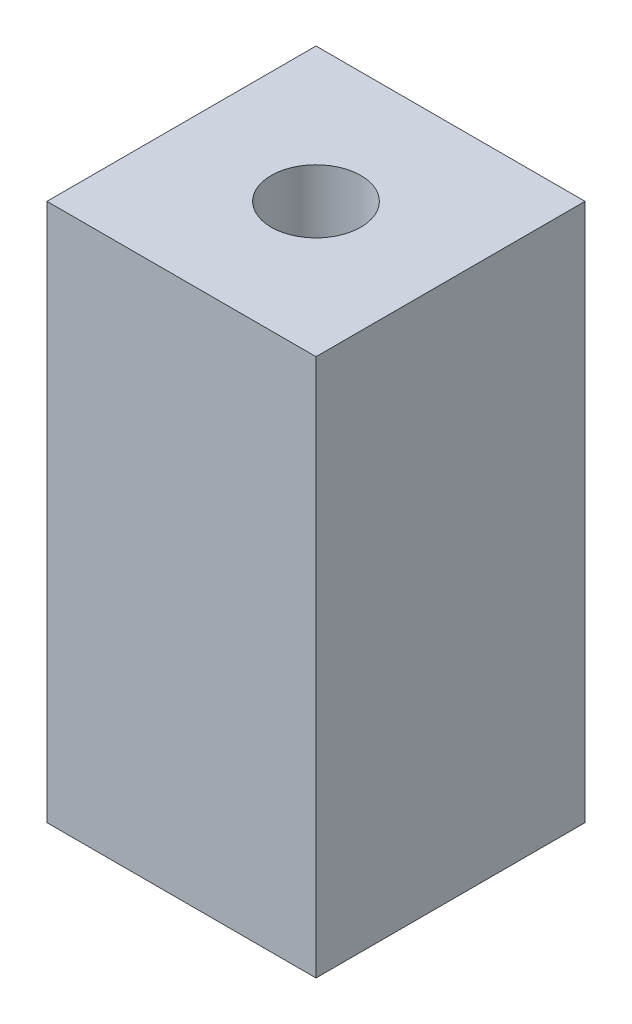
SolidWorks part; units mm, degrees
ref_plane "Front Plane" through (0, 0, 0) normal (0, 0, 1) x (1, 0, 0)
ref_plane "Top Plane" through (0, 0, 0) normal (0, 1, 0) x (1, 0, 0)
ref_plane "Right Plane" through (0, 0, 0) normal (1, 0, 0) x (0, 0, -1)
sketch "Sketch1" plane through (0, 0, 0) normal (0, 1, 0) x (1, 0, 0)
  line L1 (-9.525, -9.525) -> (9.525, -9.525)
  line L2 (-9.525, -9.525) -> (-9.525, 9.525)
  line L3 (-9.525, 9.525) -> (9.525, 9.525)
  line L4 (9.525, -9.525) -> (9.525, 9.525)
  line L5 (-9.525, -9.525) -> (9.525, 9.525) construction
  line L6 (-9.525, 9.525) -> (9.525, -9.525) construction
  circle A0 centre (0, 0) radius 3.175
  dimension "D1" = 6.35
  dimension "D3" = 19.05
  dimension "D4" = 19.05
extrude "Boss-Extrude1" add sketch "Sketch1" along normal blind 38.1
